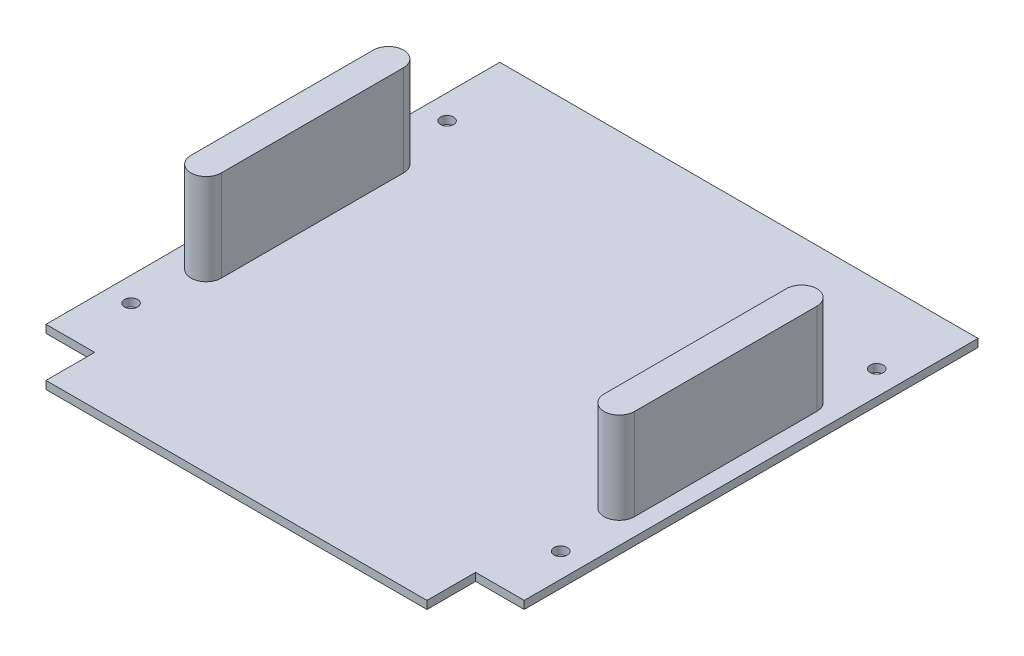
SolidWorks part; units mm, degrees
ref_plane "Front Plane" through (0, 0, 0) normal (0, 0, 1) x (1, 0, 0)
ref_plane "Top Plane" through (0, 0, 0) normal (0, 1, 0) x (1, 0, 0)
ref_plane "Right Plane" through (0, 0, 0) normal (1, 0, 0) x (0, 0, -1)
sketch "Sketch1" plane through (0, 0, 0) normal (0, 1, 0) x (1, 0, 0)
  line L0 (99.949, -101.6) -> (79.629, -101.6) construction
  line L1 (99.949, 101.6) -> (-99.949, 101.6)
  line L2 (99.949, 101.6) -> (99.949, -101.6)
  line L3 (99.949, -101.6) -> (-99.949, -101.6)
  line L4 (-99.949, 101.6) -> (-99.949, -101.6)
  line L5 (99.949, 101.6) -> (-99.949, -101.6) construction
  line L6 (99.949, -101.6) -> (-99.949, 101.6) construction
  line L7 (99.949, -101.6) -> (99.949, -81.28) construction
  line L8 (-99.949, -101.6) -> (-79.629, -101.6) construction
  line L9 (-99.949, -101.6) -> (-99.949, -81.28) construction
  line L10 (-99.949, -81.28) -> (-79.629, -81.28)
  line L11 (-79.629, -81.28) -> (-79.629, -101.6)
  line L12 (99.949, -81.28) -> (79.629, -81.28)
  line L13 (79.629, -81.28) -> (79.629, -101.6)
  point P0 (0, 0)
  dimension "D1" = 203.2
  dimension "D2" = 199.898
extrude "Boss-Extrude1" add sketch "Sketch1" along normal blind 3.302 contours L13 L12 L2 L1 L4 L10 L11 L3
sketch "Sketch3" plane through (0, 3.302, 0) normal (0, 1, 0) x (1, 0, 0)
  line L0 (-99.949, 10.16) -> (-86.36, 10.16) construction
  line L1 (-99.949, 101.6) -> (-99.949, -81.28) construction
  line L2 (99.949, 10.16) -> (86.36, 10.16) construction
  line L3 (99.949, 101.6) -> (99.949, -81.28) construction
  line L4 (86.36, 48.26) -> (86.36, -27.94) construction
  line L5 (-86.36, 48.26) -> (-86.36, -27.94) construction
  line L6 (86.36, 48.26) -> (86.36, -27.94) construction
  line L7 (92.71, 48.26) -> (92.71, -27.94)
  line L8 (80.01, 48.26) -> (80.01, -27.94)
  line L9 (-86.36, 48.26) -> (-86.36, -27.94) construction
  line L10 (-80.01, 48.26) -> (-80.01, -27.94)
  line L11 (-92.71, 48.26) -> (-92.71, -27.94)
  arc A0 (92.71, 48.26) -> (80.01, 48.26) centre (86.36, 48.26) ccw
  arc A1 (80.01, -27.94) -> (92.71, -27.94) centre (86.36, -27.94) ccw
  arc A2 (-80.01, 48.26) -> (-92.71, 48.26) centre (-86.36, 48.26) ccw
  arc A3 (-92.71, -27.94) -> (-80.01, -27.94) centre (-86.36, -27.94) ccw
  point P8 (86.36, 10.16)
  point P11 (86.36, 10.16)
  point P14 (-86.36, 10.16)
  point P19 (-86.36, 10.16)
extrude "Boss-Extrude2" add sketch "Sketch3" along normal blind 38.1
hole_wizard "M5 Clearance Hole1" positions "Sketch4" profile "Sketch5" hole size "M5" standard "ANSI Metric" end condition through all
sketch "Sketch4" plane through (0, 3.302, 0) normal (0, 1, 0) x (1, 0, 0)
  line L0 (-99.949, 101.6) -> (-99.949, -81.28) construction
  line L1 (-99.949, -81.28) -> (-79.629, -81.28) construction
  line L3 (99.949, 101.6) -> (99.949, -81.28) construction
  line L4 (99.949, 101.6) -> (-99.949, 101.6) construction
  point P0 (-89.789, -55.88)
  point P7 (-89.789, 76.2)
  point P9 (89.789, -55.88)
  point P16 (89.789, 76.2)
  dimension "D1" = 10.16
  dimension "D2" = 25.4
  dimension "D3" = 25.4
  dimension "D4" = 10.16
  dimension "D5" = 25.4
sketch "Sketch5" plane through (-89.789, 3.302, 55.88) normal (1, 0, 0) x (0, 0, 1)
  line L0 (0, 0) -> (0, 3.302)
  line L1 (0, 3.302) -> (2.75, 3.302)
  line L2 (2.75, 3.302) -> (2.75, 0)
  line L5 (2.75, 0) -> (0, 0)
  line L11 (0, -6.35) -> (0, 107.95) construction
  dimension "Thru Hole Dia." = 5.5
  dimension "Thru Hole Depth" = 3.302
sketch "Sketch6" plane through (0, 0, -101.6) normal (0, 0, -1) x (-1, 0, 0)
  line L1 (-99.949, 3.302) -> (99.949, 3.302)
  line L2 (-99.949, 3.302) -> (-99.949, 0)
  line L3 (-99.949, 0) -> (99.949, 0)
  line L4 (99.949, 3.302) -> (99.949, 0)
extrude "Boss-Extrude3" add sketch "Sketch6" along normal blind 1.62
sketch "Sketch7" plane through (0, 0, -103.22) normal (0, 0, -1) x (-1, 0, 0)
  line L1 (-99.949, 3.302) -> (99.949, 3.302)
  line L2 (-99.949, 3.302) -> (-99.949, 0)
  line L3 (-99.949, 0) -> (99.949, 0)
  line L4 (99.949, 3.302) -> (99.949, 0)
extrude "Boss-Extrude4" add sketch "Sketch7" along normal blind 5.18
